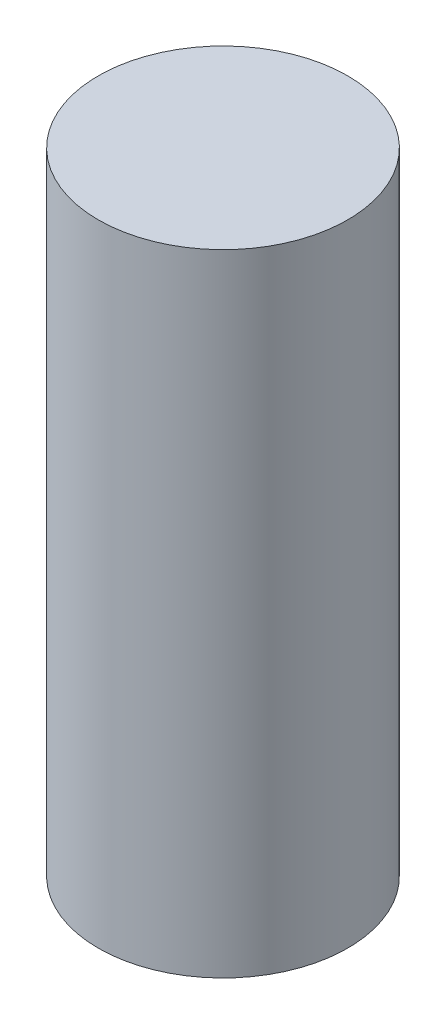
SolidWorks part; units mm, degrees
ref_plane "Front" through (0, 0, 0) normal (0, 0, 1) x (1, 0, 0)
ref_plane "Top" through (0, 0, 0) normal (0, 1, 0) x (1, 0, 0)
ref_plane "Right" through (0, 0, 0) normal (1, 0, 0) x (0, 0, -1)
sketch "Sketch1" plane through (0, 0, 0) normal (0, 1, 0) x (1, 0, 0)
  circle A0 centre (0, 0) radius 16.637
  dimension "D1" = 33.274
extrude "Boss-Extrude1" add sketch "Sketch1" along normal blind 84.1248
